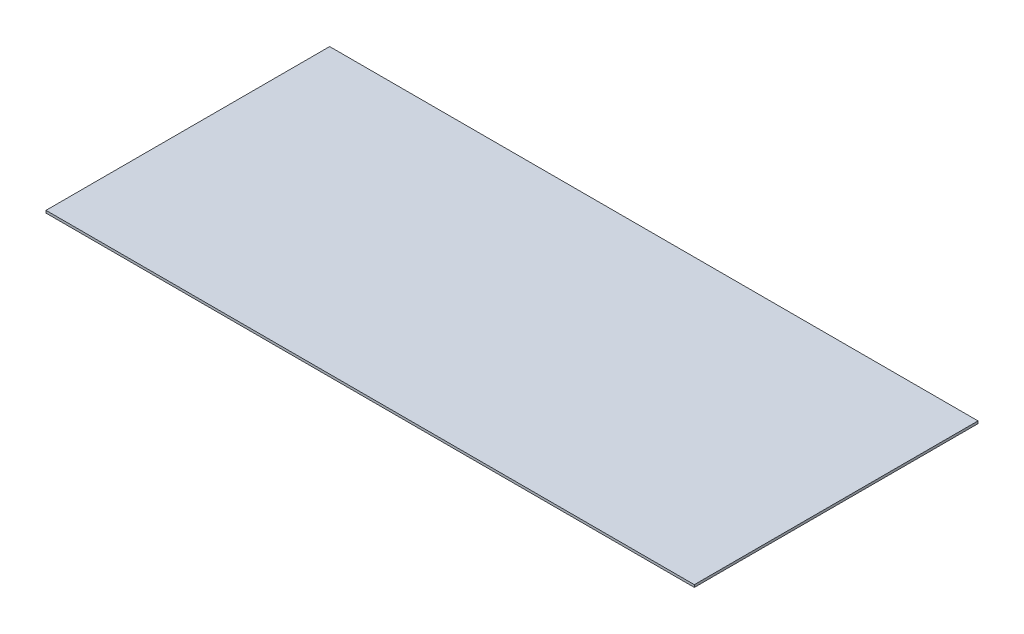
SolidWorks part; units mm, degrees
material "Very Low Density PE (SS)"
ref_plane "Alzado" through (0, 0, 0) normal (0, 0, 1) x (1, 0, 0)
ref_plane "Planta" through (0, 0, 0) normal (0, 1, 0) x (1, 0, 0)
ref_plane "Vista lateral" through (0, 0, 0) normal (1, 0, 0) x (0, 0, -1)
sketch "Sketch13" plane through (0, 0, 0) normal (0, 1, 0) x (1, 0, 0)
  line L1 (-400, -175) -> (400, -175)
  line L2 (-400, -175) -> (-400, 175)
  line L3 (-400, 175) -> (400, 175)
  line L4 (400, -175) -> (400, 175)
  line L5 (-400, -175) -> (400, 175) construction
  line L6 (-400, 175) -> (400, -175) construction
  point P0 (0, 0)
  dimension "D1" = 800
  dimension "D2" = 350
extrude "Boss-Extrude1" add sketch "Sketch13" along normal blind 3
